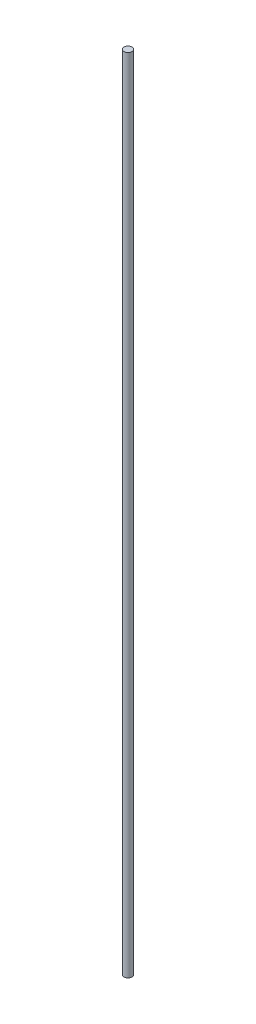
SolidWorks part; units mm, degrees
ref_plane "前视基准面" through (0, 0, 0) normal (0, 0, 1) x (1, 0, 0)
ref_plane "上视基准面" through (0, 0, 0) normal (0, 1, 0) x (1, 0, 0)
ref_plane "右视基准面" through (0, 0, 0) normal (1, 0, 0) x (0, 0, -1)
sketch "草图1" plane through (0, 0, 0) normal (0, 1, 0) x (1, 0, 0)
  circle A0 centre (0, 0) radius 1
extrude "凸台-拉伸1" add sketch "草图1" along normal blind 200
sketch "草图2" plane through (0, 200, 0) normal (0, 1, 0) x (1, 0, 0)
  point P0 (0, 0)
sketch "草图3" plane through (0, 0, 0) normal (0, -1, 0) x (1, 0, 0)
  point P0 (0, 0)
